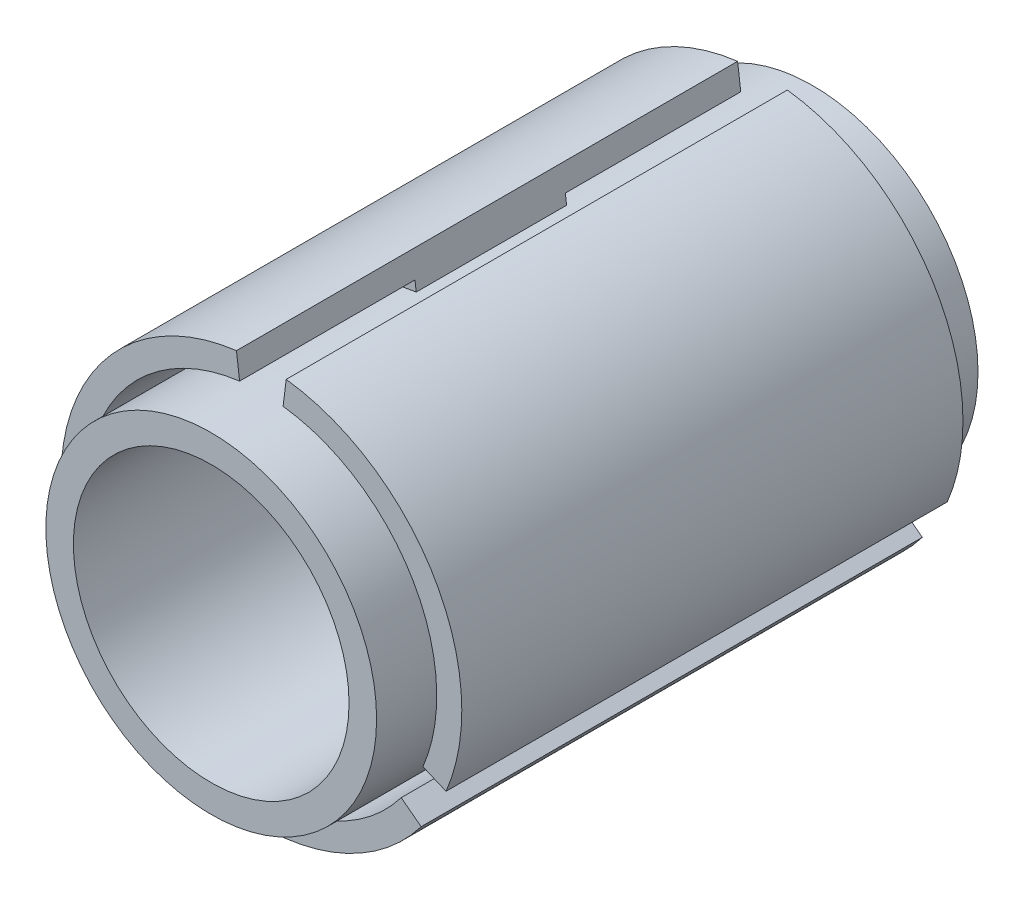
SolidWorks part; units mm, degrees
ref_plane "Alzado" through (0, 0, 0) normal (0, 0, 1) x (1, 0, 0)
ref_plane "Planta" through (0, 0, 0) normal (0, 1, 0) x (1, 0, 0)
ref_plane "Vista lateral" through (0, 0, 0) normal (1, 0, 0) x (0, 0, -1)
sketch "Croquis1" plane through (0, 0, 0) normal (0, 0, 1) x (1, 0, 0)
  circle A0 centre (0, 0) radius 33
  dimension "D1" = 66
extrude "Saliente-Extruir1" add sketch "Croquis1" along normal mid plane 30
sketch "Croquis2" plane through (0, 0, 0) normal (0, 0, 1) x (1, 0, 0)
  line L0 (0, 0) -> (0, 40) construction
  line L1 (0, 0) -> (-5, 40) construction
  line L2 (0, 0) -> (5, 40) construction
  line L4 (-4.9614, 39.6911) -> (-4.0931, 32.7452)
  line L5 (4.9614, 39.6911) -> (4.0931, 32.7452)
  line L6 (31.8928, -24.1422) -> (26.3116, -19.9174)
  line L7 (36.8542, -15.5489) -> (30.4047, -12.8278)
  line L8 (-36.8542, -15.5489) -> (-30.4047, -12.8278)
  line L9 (-31.8928, -24.1422) -> (-26.3116, -19.9174)
  arc A0 (-4.9614, 39.6911) -> (-36.8542, -15.5489) centre (0, 0) ccw
  circle A1 centre (0, 0) radius 33 construction
  arc A2 (-4.0931, 32.7452) -> (-30.4047, -12.8278) centre (0, 0) ccw
  arc A3 (30.4047, -12.8278) -> (4.0931, 32.7452) centre (0, 0) ccw
  arc A4 (36.8542, -15.5489) -> (4.9614, 39.6911) centre (0, 0) ccw
  arc A5 (-31.8928, -24.1422) -> (31.8928, -24.1422) centre (0, 0) ccw
  arc A6 (-26.3116, -19.9174) -> (26.3116, -19.9174) centre (0, 0) ccw
  point P24 (0, 0)
  dimension "D1" = 10
  dimension "D2" = 5
  dimension "D3" = 40
  dimension "D4" = 3
extrude "Saliente-Extruir2" add sketch "Croquis2" along normal mid plane 30
sketch "Croquis3" plane through (0, 0, 0) normal (0, 0, 1) x (1, 0, 0)
  line L0 (-4.3412, 34.7297) -> (-4.9614, 39.6911)
  line L1 (-4.0931, 32.7452) -> (-4.9614, 39.6911) construction
  line L2 (4.3412, 34.7297) -> (4.9614, 39.6911)
  line L3 (32.2474, -13.6053) -> (36.8542, -15.5489)
  line L4 (30.4047, -12.8278) -> (36.8542, -15.5489) construction
  line L5 (31.8928, -24.1422) -> (27.9062, -21.1245)
  line L6 (31.8928, -24.1422) -> (26.3116, -19.9174) construction
  line L7 (-31.8928, -24.1422) -> (-27.9062, -21.1245)
  line L8 (-26.3116, -19.9174) -> (-31.8928, -24.1422) construction
  line L9 (-36.8542, -15.5489) -> (-32.2474, -13.6053)
  line L10 (-36.8542, -15.5489) -> (-30.4047, -12.8278) construction
  arc A0 (-4.3412, 34.7297) -> (-32.2474, -13.6053) centre (0, 0) ccw
  arc A1 (-4.9614, 39.6911) -> (-36.8542, -15.5489) centre (0, 0) ccw
  arc A2 (32.2474, -13.6053) -> (4.3412, 34.7297) centre (0, 0) ccw
  arc A3 (36.8542, -15.5489) -> (4.9614, 39.6911) centre (0, 0) ccw
  arc A4 (-27.9062, -21.1245) -> (27.9062, -21.1245) centre (0, 0) ccw
  arc A5 (-31.8928, -24.1422) -> (31.8928, -24.1422) centre (0, 0) ccw
  dimension "D1" = 70
extrude "Saliente-Extruir3" add sketch "Croquis3" along normal mid plane 100
sketch "Croquis4" plane through (0, 0, 0) normal (0, 0, 1) x (1, 0, 0)
  circle A0 centre (0, 0) radius 33
  dimension "D1" = 66
extrude "Saliente-Extruir4" add sketch "Croquis4" along normal mid plane 120
sketch "Croquis5" plane through (0, 0, 60) normal (0, 0, 1) x (1, 0, 0)
  circle A0 centre (0, 0) radius 27.5
  dimension "D1" = 55
extrude "Cortar-Extruir1" cut sketch "Croquis5" against normal blind 40
sketch "Croquis6" plane through (0, 0, -60) normal (0, 0, -1) x (-1, 0, 0)
  circle A0 centre (0, 0) radius 27.5
  dimension "D1" = 55
extrude "Cortar-Extruir2" cut sketch "Croquis6" against normal blind 75
sketch "Croquis7" plane through (0, 0, 0) normal (0, 0, 1) x (1, 0, 0)
  line L0 (5, -5) -> (-5, 5) construction
  line L1 (-5, 5) -> (5, 5) construction
  line L2 (5, 5) -> (-5, -5) construction
  circle A0 centre (5, 5) radius 1
  circle A1 centre (-5, 5) radius 1
  circle A2 centre (-5, -5) radius 1
  circle A3 centre (5, -5) radius 1
  point P0 (0, 0)
  point P6 (0, 0)
  dimension "D3" = 2
  dimension "D1" = 10
  dimension "D2" = 10
extrude "Cortar-Extruir3" cut sketch "Croquis7" against normal through all both and the other way through all
